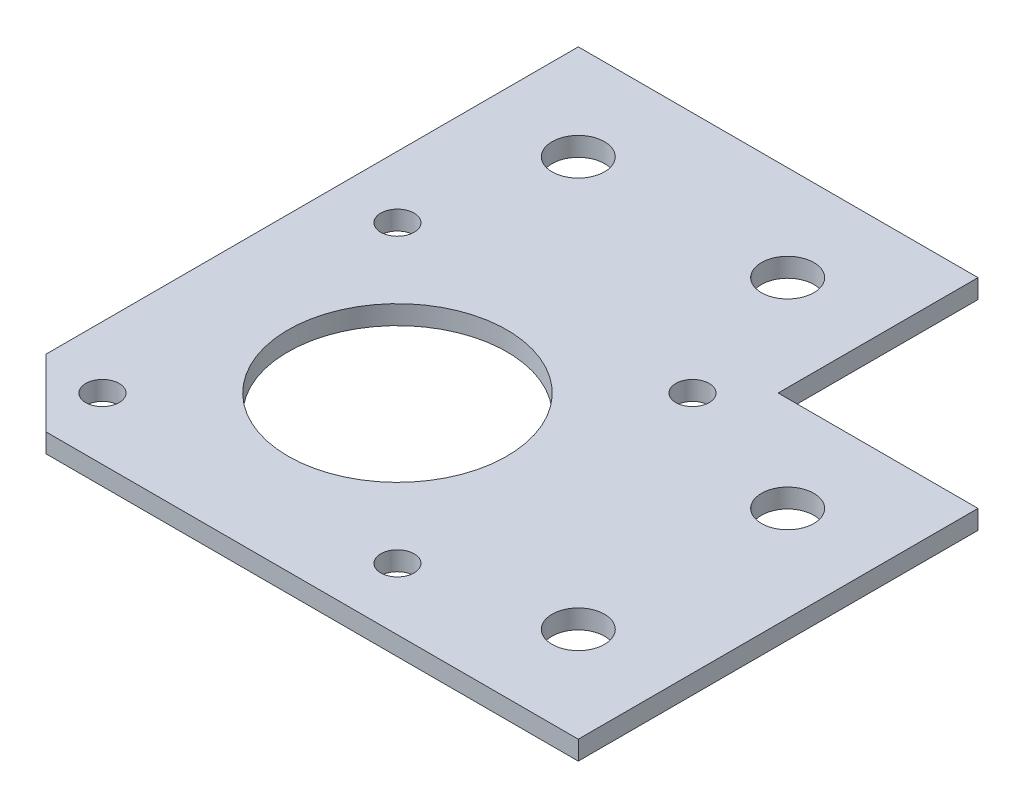
SolidWorks part; units mm, degrees
ref_plane "前视基准面" through (0, 0, 0) normal (0, 0, 1) x (1, 0, 0)
ref_plane "上视基准面" through (0, 0, 0) normal (0, 1, 0) x (1, 0, 0)
ref_plane "右视基准面" through (0, 0, 0) normal (1, 0, 0) x (0, 0, -1)
sketch "草图1" plane through (0, 0, 0) normal (0, 1, 0) x (1, 0, 0)
  line L0 (0, 0) -> (0, 68.5567) construction
  line L1 (0, 0) -> (34.2784, 0) construction
  line L2 (-63, 0) -> (-63, -63)
  line L3 (-63, -63) -> (0, -63)
  line L4 (-63, 0) -> (-21, 0)
  line L5 (-21, 0) -> (-21, -21)
  line L8 (-21, -21) -> (0, -21)
  line L9 (0, -63) -> (0, -21)
  dimension "D1" = 42
  dimension "D2" = 42
  dimension "D3" = 21
  dimension "D4" = 21
extrude "凸台-拉伸1" add sketch "草图1" along normal blind 2
sketch "草图3" plane through (0, 2, 0) normal (0, 1, 0) x (1, 0, 0)
  line L0 (-63, 0) -> (-63, -63) construction
  line L1 (-21, 0) -> (-63, 0) construction
  line L2 (-53, -10) -> (-10, -10) construction
  line L3 (-10, -10) -> (-10, -59.8108) construction
  line L4 (0, -63) -> (0, -21) construction
  line L5 (-92.7463, -41) -> (-40.5568, -41) construction
  line L6 (-41, -28.1152) -> (-41, -55.9496) construction
  line L7 (-63, -63) -> (0, -63) construction
  line L8 (-63, -63) -> (-63, -55.9289)
  line L9 (-63, -63) -> (-55.9289, -63)
  line L10 (-63, -55.9289) -> (-55.9289, -63)
  line L14 (0, -21) -> (-21, -21) construction
  line L15 (-21, -21) -> (-21, 0) construction
  circle A0 centre (-53, -10) radius 2.75
  circle A6 centre (-56.5, -56.5) radius 1.75
  circle A7 centre (-25.5, -56.5) radius 1.75
  circle A8 centre (-25.5, -25.5) radius 1.75
  circle A9 centre (-56.5, -25.5) radius 1.75
  circle A10 centre (-41, -41) radius 11.5
  circle A11 centre (-10, -53) radius 2.75
  circle A12 centre (-10, -31) radius 2.75
  circle A13 centre (-31, -10) radius 2.75
  point P19 (-10, -10)
  point P20 (-10, -10)
  point P36 (-41, -41)
  point P43 (-41, -41)
  dimension "D1" = 5.5
  dimension "D9" = 3.5
  dimension "D17" = 23
  dimension "D16" = 5.5
  dimension "D18" = 5.5
  dimension "D19" = 5.5
  dimension "D2" = 10
  dimension "D3" = 10
  dimension "D5" = 10
  dimension "D7" = 22
  dimension "D8" = 22
  dimension "D10" = 15.5
  dimension "D11" = 15.5
  dimension "D14" = 45
  dimension "D15" = 10
  dimension "D4" = 10
  dimension "D6" = 10
  dimension "D20" = 10
  dimension "D12" = 2
  dimension "D13" = 2
extrude "切除-拉伸1" cut sketch "草图3" against normal through all
sketch "草图4" plane through (0, 2, 0) normal (0, 1, 0) x (1, 0, 0)
  line L2 (-55.9289, -63) -> (-63, -55.9289) construction
  line L3 (-18, -63) -> (39.5601, -63) construction
  line L5 (-63, -64.8122) -> (-63, -92.2969) construction
  line L7 (-24.5744, 25.8537) -> (104.1994, -102.9202) construction
  line L8 (-63, 0) -> (-63, -55.9289) construction
  line L9 (-55.9289, -63) -> (0, -63) construction
  dimension "D1" = 85
